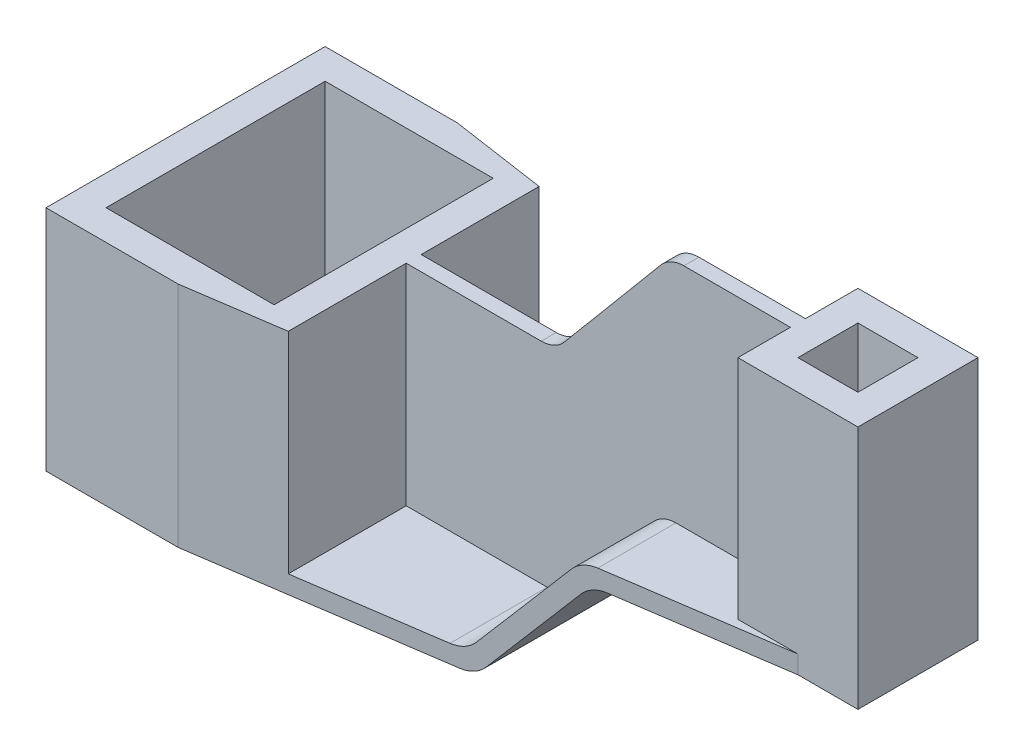
SolidWorks part; units mm, degrees
material "1060 Legierung"
ref_plane "Ebene vorne" through (0, 0, 0) normal (0, 0, 1) x (1, 0, 0)
ref_plane "Ebene oben" through (0, 0, 0) normal (0, 1, 0) x (1, 0, 0)
ref_plane "Ebene rechts" through (0, 0, 0) normal (1, 0, 0) x (0, 0, -1)
sketch "Skizze1" plane through (0, 0, 0) normal (0, 1, 0) x (1, 0, 0)
  line L0 (-38, 46.5) -> (-38, -46.5)
  line L1 (-38, -46.5) -> (38, -46.5)
  line L2 (38, -46.5) -> (38, 46.5)
  line L3 (38, 46.5) -> (-38, 46.5)
  point P7 (-54.9679, -12.3957)
  point P9 (-34.8503, 17.8824)
  dimension "D1" = 76
  dimension "D2" = 46.5
  dimension "D3" = 46.5
  dimension "D4" = 38
extrude "Aufsatz-Linear austragen1" add sketch "Skizze1" along normal blind 76
sketch "Skizze2" plane through (0, 0, 0) normal (0, 0, 1) x (1, 0, 0)
  line L0 (38, 0) -> (92.436, 0)
  line L1 (92.436, 0) -> (126, 40)
  line L2 (126, 40) -> (186, 40)
  line L3 (38, 6) -> (89.6382, 6)
  line L4 (89.6382, 6) -> (123.2022, 46)
  line L5 (123.2022, 46) -> (186, 46)
  line L6 (38, 0) -> (38, 6)
  line L7 (0, 6) -> (89.6382, 6) construction
  line L8 (0, 0) -> (92.436, 0) construction
  line L9 (186, 46) -> (186, 40)
  dimension "D1" = 40
  dimension "D2" = 60
  dimension "D4" = 130
  dimension "D5" = 186
  dimension "D3" = 6
extrude "Aufsatz-Linear austragen2" add sketch "Skizze2" along normal mid plane 93
sketch "Skizze3" plane through (0, 40, 0) normal (0, -1, 0) x (1, 0, 0)
  line L0 (0, 0) -> (186, 0) construction
  line L5 (166, -20) -> (206, -20)
  line L6 (166, -20) -> (166, 20)
  line L7 (166, 20) -> (206, 20)
  line L8 (206, -20) -> (206, 20)
  line L9 (166, -20) -> (206, 20) construction
  line L10 (166, 20) -> (206, -20) construction
  point P0 (186, 0)
  dimension "D1" = 40
  dimension "D2" = 186
extrude "Aufsatz-Linear austragen3" add sketch "Skizze3" against normal blind 81.5
sketch "Skizze4" plane through (0, 0, 0) normal (0, 0, 1) x (1, 0, 0)
  line L0 (38, 76) -> (87.6737, 76)
  line L1 (87.6737, 76) -> (125.8527, 121.5)
  line L2 (125.8527, 121.5) -> (166, 121.5)
  line L3 (123.2022, 46) -> (89.6382, 6) construction
  line L4 (123.2022, 46) -> (89.6382, 6)
  line L5 (166, 121.5) -> (166, 46) construction
  line L6 (186, 46) -> (123.2022, 46) construction
  line L7 (89.6382, 6) -> (38, 6) construction
  line L8 (38, 76) -> (38, 6) construction
  line L9 (166, 121.5) -> (166, 46)
  line L10 (166, 46) -> (123.2022, 46)
  line L11 (89.6382, 6) -> (38, 6)
  line L12 (38, 76) -> (38, 6)
  dimension "D1" = 46.5
extrude "Aufsatz-Linear austragen4" add sketch "Skizze4" along normal mid plane 5
sketch "Skizze5" plane through (0, 121.5, 0) normal (0, 1, 0) x (1, 0, 0)
  line L0 (176, 10) -> (176, -10)
  line L5 (176, -10) -> (196, -10)
  line L6 (196, -10) -> (196, 10)
  line L7 (196, 10) -> (176, 10)
  line L12 (206, -20) -> (206, 20)
  line L13 (206, 20) -> (166, 20)
  line L14 (166, 20) -> (166, 2.5)
  line L15 (166, 2.5) -> (125.8527, 2.5)
  line L16 (125.8527, 2.5) -> (125.8527, -2.5)
  line L17 (125.8527, -2.5) -> (166, -2.5)
  line L18 (166, -2.5) -> (166, -20)
  line L19 (166, -20) -> (206, -20)
  line L20 (206, -20) -> (206, 20)
  line L21 (206, 20) -> (166, 20)
  line L22 (166, 20) -> (166, 2.5)
  line L23 (166, 2.5) -> (125.8527, 2.5)
  line L24 (125.8527, 2.5) -> (125.8527, -2.5)
  line L25 (125.8527, -2.5) -> (166, -2.5)
  line L26 (166, -2.5) -> (166, -20)
  line L27 (166, -20) -> (206, -20)
  line L28 (176, -2.5) -> (176, -10) construction
  line L29 (176, 10) -> (176, 2.5) construction
  dimension "D1" = 0
  dimension "D2" = 10
extrude "Schnitt-Linear austragen1" cut sketch "Skizze5" against normal through all
sketch "Skizze6" plane through (0, 76, 0) normal (0, 1, 0) x (1, 0, 0)
  line L16 (28, 36.5) -> (-28, 36.5)
  line L17 (-28, 36.5) -> (-28, -36.5)
  line L18 (-28, -36.5) -> (28, -36.5)
  line L19 (28, -36.5) -> (28, 36.5)
  line L20 (28, 36.5) -> (-28, 36.5)
  line L21 (-28, 36.5) -> (-28, -36.5)
  line L22 (-28, -36.5) -> (28, -36.5)
  line L23 (28, -36.5) -> (28, 36.5)
  dimension "D1" = 10
extrude "Schnitt-Linear austragen2" cut sketch "Skizze6" against normal through all contours L20 L21 L22 L23
sketch "Skizze7" plane through (0, 121.5, 0) normal (0, 1, 0) x (1, 0, 0)
  line L0 (6, 46.5) -> (186, 20)
  line L1 (38, 46.5) -> (-38, 46.5) construction
  line L2 (186, 20) -> (186, 46.5)
  line L3 (186, 46.5) -> (6, 46.5)
  line L4 (6, -46.5) -> (186, -20)
  line L5 (-38, -46.5) -> (38, -46.5) construction
  line L6 (186, -20) -> (186, -46.5)
  line L7 (186, -46.5) -> (6, -46.5)
  dimension "D1" = 6
  dimension "D2" = 6
extrude "Schnitt-Linear austragen3" cut sketch "Skizze7" against normal through all
fillet "Verrundung1" radius 10 8 edges at (126, 40, 0) (92.436, 0, 0) (123.2022, 46, -15.8726) (89.6382, 6, -18.3433) (123.2022, 46, 15.8726) (89.6382, 6, 18.3433) (125.8527, 121.5, 0) (87.6737, 76, 0)
equation "\"A\"= 186mm"
equation "\"B\"= 76mm"
equation "\"W\" = \"B\" / 2"
equation "\"X\"= \"A\" / 4"
equation "\"Y\"= \"B\" + 5.5mm"
equation "\"D1@Skizze1\"= \"B\""
equation "\"D4@Skizze1\"= \"W\""
equation "\"D2@Skizze1\"= \"X\""
equation "\"D3@Skizze1\"= \"X\""
equation "\"D1@Aufsatz-Linear austragen1\"= \"B\""
equation "\"D5@Skizze2\"= \"A\""
equation "\"D1@Aufsatz-Linear austragen2\"= \"X\" * 2"
equation "\"D2@Skizze3\"= \"A\""
equation "\"D1@Aufsatz-Linear austragen3\"= \"Y\""
